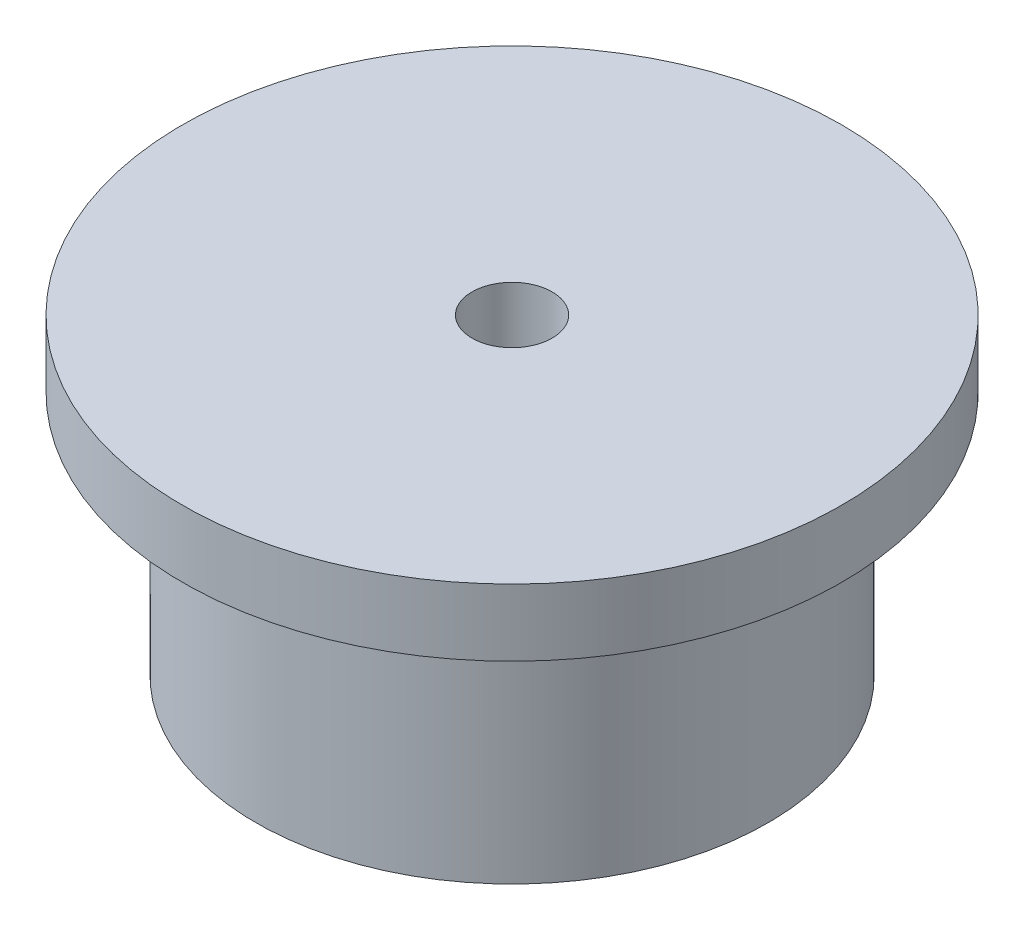
SolidWorks part; units mm, degrees
ref_plane "Front Plane" through (0, 0, 0) normal (0, 0, 1) x (1, 0, 0)
ref_plane "Top Plane" through (0, 0, 0) normal (0, 1, 0) x (1, 0, 0)
ref_plane "Right Plane" through (0, 0, 0) normal (1, 0, 0) x (0, 0, -1)
sketch "Sketch2" plane through (0, 0, 0) normal (1, 0, 0) x (0, 0, -1)
  line L0 (0, 0) -> (0, 119.5399) construction
  line L1 (17.5, 24) -> (17.5, 64)
  line L2 (17.5, 64) -> (25, 64)
  line L3 (25, 64) -> (25, 74)
  line L4 (25, 74) -> (9, 74)
  line L5 (9, 74) -> (9, 94)
  line L6 (9, 94) -> (74, 94)
  line L7 (74, 94) -> (74, 79)
  line L8 (74, 79) -> (57.5, 79)
  line L9 (57.5, 79) -> (57.5, 24)
  line L10 (57.5, 24) -> (17.5, 24)
  point P15 (50.514, 3.1833)
  dimension "D1" = 9
  dimension "D2" = 17.5
  dimension "D3" = 25
  dimension "D4" = 40
  dimension "D5" = 10
  dimension "D6" = 15
  dimension "D7" = 65
  dimension "D8" = 20
  dimension "D9" = 40
  dimension "D10" = 24
revolve "Revolve1" add sketch "Sketch2" angle 360 about L0
